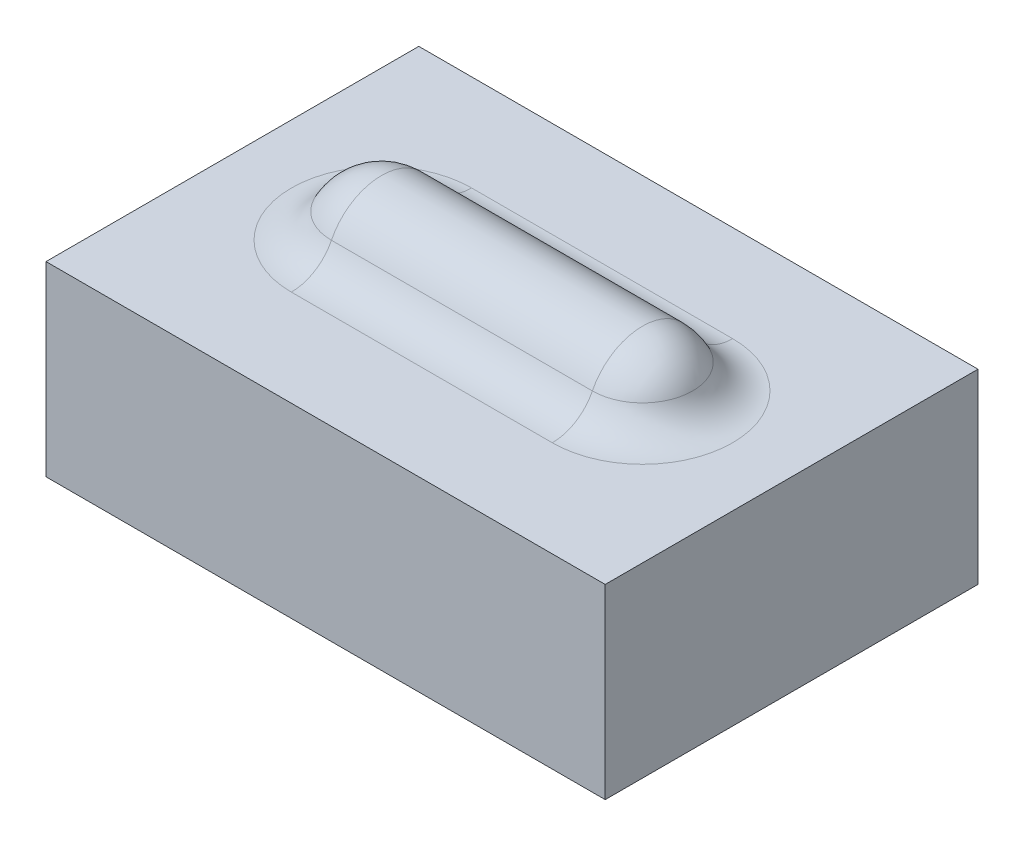
SolidWorks part; units mm, degrees
ref_plane "前视基准面" through (0, 0, 0) normal (0, 0, 1) x (1, 0, 0)
ref_plane "上视基准面" through (0, 0, 0) normal (0, 1, 0) x (1, 0, 0)
ref_plane "右视基准面" through (0, 0, 0) normal (1, 0, 0) x (0, 0, -1)
sketch "草图1" plane through (0, 0, 0) normal (0, 1, 0) x (1, 0, 0)
  line L1 (-7.5, 5) -> (7.5, 5)
  line L2 (-7.5, 5) -> (-7.5, -5)
  line L3 (-7.5, -5) -> (7.5, -5)
  line L4 (7.5, 5) -> (7.5, -5)
  line L5 (-7.5, 5) -> (7.5, -5) construction
  line L6 (-7.5, -5) -> (7.5, 5) construction
  point P0 (0, 0)
  dimension "D1" = 10
  dimension "D2" = 15
extrude "凸台-拉伸1" add sketch "草图1" along normal blind 5
sketch "草图2" plane through (0, 0, 0) normal (0, 0, 1) x (1, 0, 0)
  line L0 (-7.5, 5) -> (7.5, 5) construction
  line L1 (0, 0) -> (0, 7.2395) construction
  line L2 (-3.5, 5) -> (3.5, 5) construction
  line L3 (-3.5, 6.5) -> (3.5, 6.5)
  line L5 (-5, 5) -> (5, 5)
  arc A0 (-3.5, 6.5) -> (-5, 5) centre (-3.5, 5) ccw
  arc A1 (5, 5) -> (3.5, 6.5) centre (3.5, 5) ccw
  point P9 (-0.2049, 5)
  dimension "D1" = 1.5
  dimension "D2" = 10
revolve "旋转1" add sketch "草图2" angle 360 about L0
fillet "圆角1" radius 1.2 4 edges at (5, 5, 0) (0, 5, -1.5) (0, 5, 1.5) (-5, 5, 0)
sketch "方向草图" plane through (0, 5, 0) normal (0, 1, 0) x (1, 0, 0)
  line L0 (-3.5, 2.4187) -> (3.5, 2.4187) construction
  line L1 (3.5, -2.4187) -> (-3.5, -2.4187) construction
  line L2 (7.5, -5) -> (7.5, 5) construction
  line L3 (7.5, 5) -> (-7.5, 5) construction
  line L4 (-7.5, 5) -> (-7.5, -5) construction
  line L5 (-7.5, -5) -> (7.5, -5) construction
  line L6 (-3.5, 2.4187) -> (3.5, 2.4187)
  line L7 (3.5, -2.4187) -> (-3.5, -2.4187)
  line L8 (7.5, -5) -> (7.5, 5) construction
  line L9 (7.5, 5) -> (-7.5, 5) construction
  line L10 (-7.5, 5) -> (-7.5, -5) construction
  line L11 (-7.5, -5) -> (7.5, -5) construction
  arc A0 (3.5, -2.4187) -> (3.5, 2.4187) centre (3.5, 0) ccw construction
  arc A1 (-3.5, 2.4187) -> (-3.5, -2.4187) centre (-3.5, 0) ccw construction
  arc A2 (3.5, -2.4187) -> (3.5, 2.4187) centre (3.5, 0) ccw
  arc A3 (-3.5, 2.4187) -> (-3.5, -2.4187) centre (-3.5, 0) ccw
  point P8 (0, 0)
other "成形工具1"
